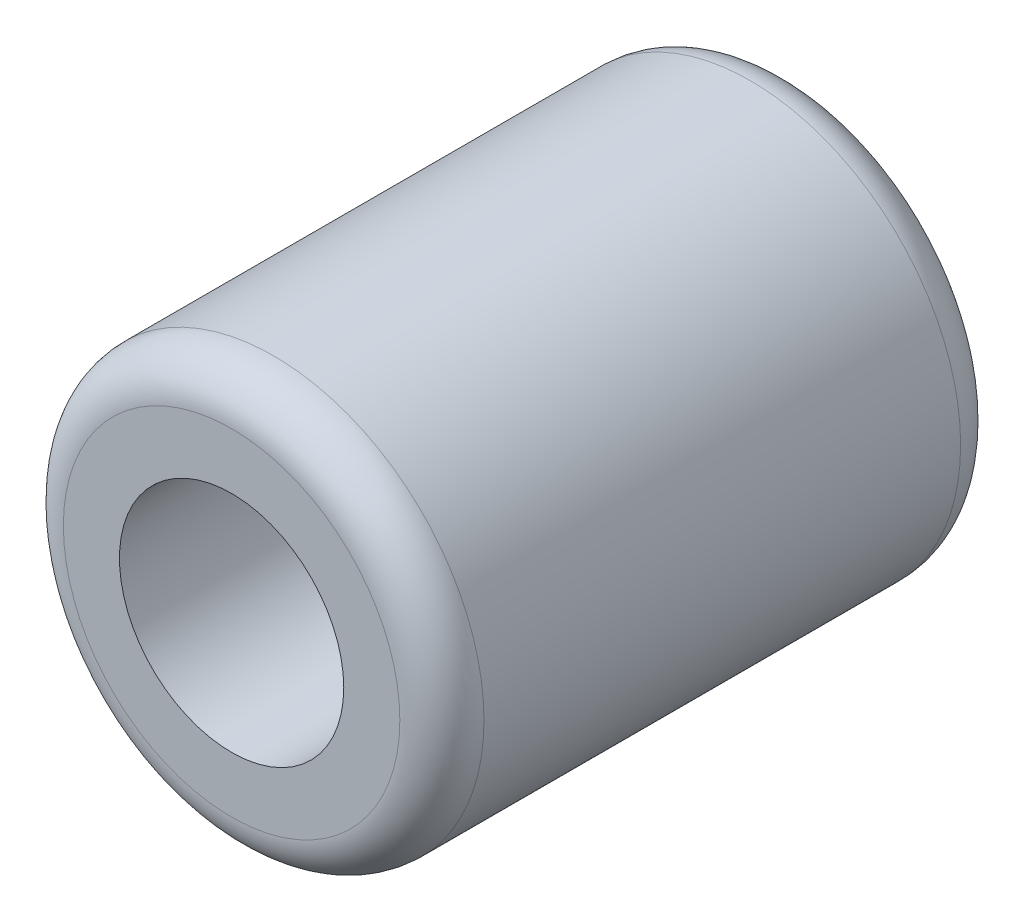
SolidWorks part; units mm, degrees
material "AISI 1020"
ref_plane "Спереди" through (0, 0, 0) normal (0, 0, 1) x (1, 0, 0)
ref_plane "Сверху" through (0, 0, 0) normal (0, 1, 0) x (1, 0, 0)
ref_plane "Справа" through (0, 0, 0) normal (1, 0, 0) x (0, 0, -1)
sketch "Эскиз1" plane through (0, 0, 0) normal (0, 0, 1) x (1, 0, 0)
  circle A0 centre (0, 0) radius 8
  circle A1 centre (0, 0) radius 15
  dimension "D1" = 16
  dimension "D2" = 30
extrude "Бобышка-Вытянуть1" add sketch "Эскиз1" along normal mid plane 40
fillet "Скругление1" radius 3 2 edges at (15, 0, -20) (15, 0, 20)
